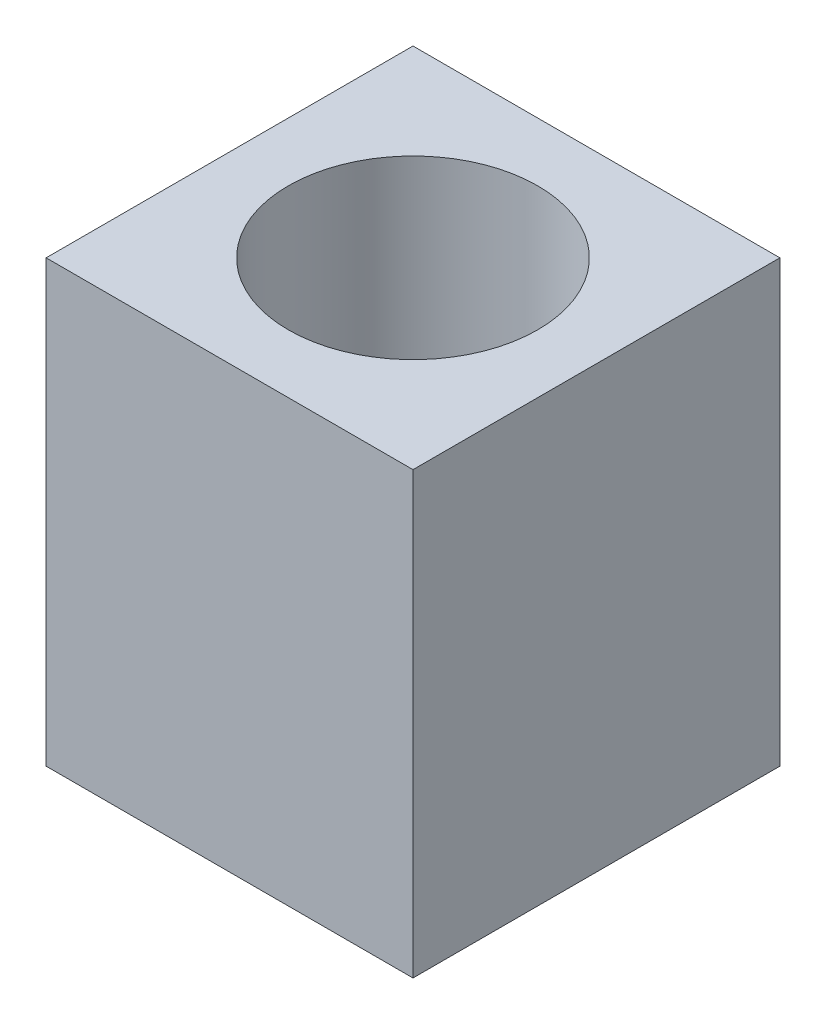
SolidWorks part; units mm, degrees
ref_plane "Front Plane" through (0, 0, 0) normal (0, 0, 1) x (1, 0, 0)
ref_plane "Top Plane" through (0, 0, 0) normal (0, 1, 0) x (1, 0, 0)
ref_plane "Right Plane" through (0, 0, 0) normal (1, 0, 0) x (0, 0, -1)
sketch "Sketch1" plane through (0, 0, 0) normal (0, 1, 0) x (1, 0, 0)
  line L1 (-2.5, -2.5) -> (2.5, -2.5)
  line L2 (-2.5, -2.5) -> (-2.5, 2.5)
  line L3 (-2.5, 2.5) -> (2.5, 2.5)
  line L4 (2.5, -2.5) -> (2.5, 2.5)
  line L5 (-2.5, -2.5) -> (2.5, 2.5) construction
  line L6 (-2.5, 2.5) -> (2.5, -2.5) construction
  circle A0 centre (0, 0) radius 1.7
  dimension "D1" = 3.4
  dimension "D2" = 5
extrude "Boss-Extrude1" add sketch "Sketch1" along normal blind 6
